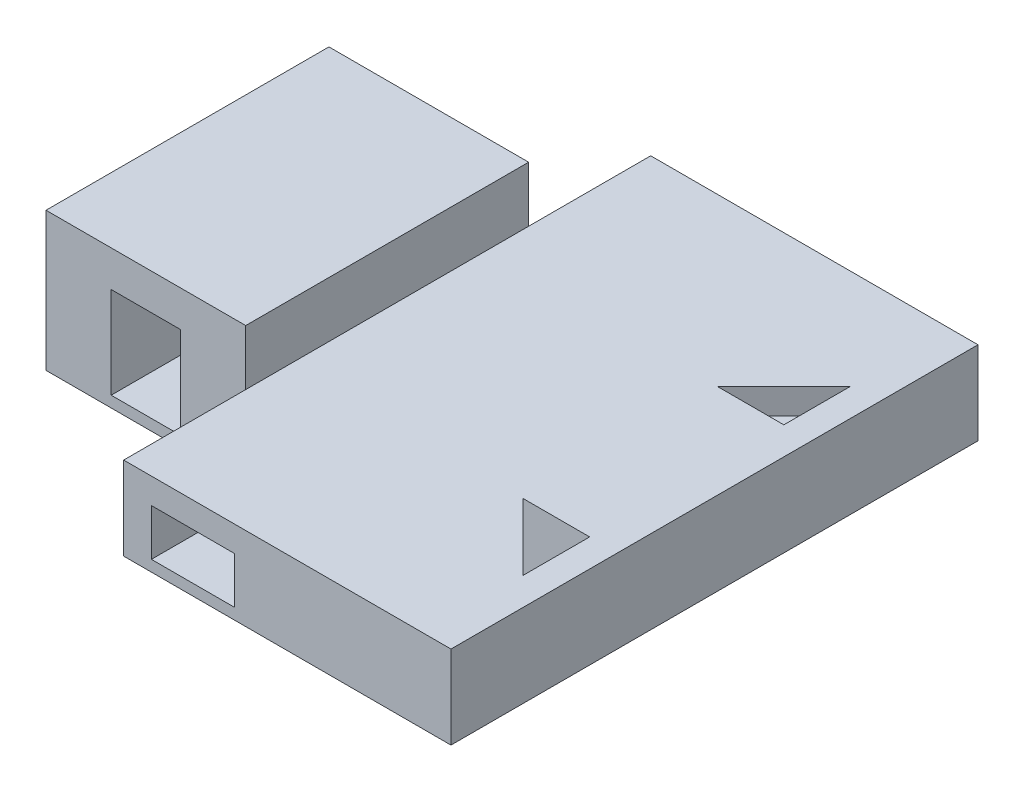
SolidWorks part; units mm, degrees
ref_plane "Front Plane" through (0, 0, 0) normal (0, 0, 1) x (1, 0, 0)
ref_plane "Top Plane" through (0, 0, 0) normal (0, 1, 0) x (1, 0, 0)
ref_plane "Right Plane" through (0, 0, 0) normal (1, 0, 0) x (0, 0, -1)
sketch "Sketch1" plane through (0, 0, 0) normal (0, 1, 0) x (1, 0, 0)
  line L1 (-45, -47.5) -> (45, -47.5)
  line L2 (-45, -47.5) -> (-45, 47.5)
  line L3 (-45, 47.5) -> (45, 47.5)
  line L4 (45, -47.5) -> (45, 47.5)
  line L5 (-45, -47.5) -> (45, 47.5) construction
  line L6 (-45, 47.5) -> (45, -47.5) construction
  point P0 (0, 0)
  dimension "D1" = 95
  dimension "D2" = 90
extrude "Boss-Extrude3" add sketch "Sketch1" along normal blind 15
sketch "Sketch5" plane through (45, 0, 0) normal (1, 0, 0) x (0, 0, -1)
  line L0 (-47.5, 0) -> (47.5, 0) construction
  line L1 (-6.6, 2) -> (8.4, 2)
  line L2 (-6.6, 2) -> (-6.6, 10.4)
  line L3 (-6.6, 10.4) -> (8.4, 10.4)
  line L4 (8.4, 2) -> (8.4, 10.4)
  dimension "D1" = 15
  dimension "D2" = 8.4
  dimension "D3" = 2
extrude "Cut-Extrude3" cut sketch "Sketch5" against normal blind 40
sketch "Sketch7" plane through (45, 0, 0) normal (1, 0, 0) x (0, 0, -1)
  line L1 (-47.5, 0) -> (47.5, 0)
  line L2 (-47.5, 0) -> (-47.5, 15)
  line L3 (-47.5, 15) -> (47.5, 15)
  line L4 (47.5, 0) -> (47.5, 15)
extrude "Boss-Extrude4" add sketch "Sketch7" along normal blind 5
sketch "Sketch10" plane through (0, 15, 0) normal (0, 1, 0) x (1, 0, 0)
  line L0 (50, 47.5) -> (50, -47.5) construction
  line L3 (33, -17.5) -> (45, -17.5)
  line L4 (45, -29.5) -> (45, -17.5)
  line L6 (45, -29.5) -> (33, -17.5)
  dimension "D3" = 5
extrude "Cut-Extrude7" cut sketch "Sketch10" against normal blind 13
sketch "Sketch12" plane through (7.75, 0, -7.75) normal (0.7071, 0, -0.7071) x (-0.7071, 0, -0.7071)
  line L0 (-35.7089, 2) -> (-35.7089, 15) construction
  line L1 (-36.7089, 10.4) -> (-51.7089, 10.4)
  line L2 (-36.7089, 10.4) -> (-36.7089, 2)
  line L3 (-36.7089, 2) -> (-51.7089, 2)
  line L4 (-51.7089, 10.4) -> (-51.7089, 2)
  line L5 (-35.7089, 2) -> (-52.6795, 2) construction
  dimension "D1" = 15
  dimension "D2" = 8.4
  dimension "D3" = 1
  dimension "D4" = 0
extrude "Cut-Extrude8" cut sketch "Sketch12" against normal blind 20
sketch "Sketch13" plane through (0, 15, 0) normal (0, 1, 0) x (1, 0, 0)
  line L0 (50, 47.5) -> (50, -47.5) construction
  line L1 (33, 17.5) -> (45, 17.5)
  line L4 (45, 17.5) -> (45, 29.5)
  line L5 (50, 47.5) -> (-45, 47.5) construction
  line L6 (33, 17.5) -> (45, 29.5)
  dimension "D3" = 5
  dimension "D4" = 18
extrude "Cut-Extrude9" cut sketch "Sketch13" against normal blind 13
sketch "Sketch14" plane through (7.75, 0, 7.75) normal (0.7071, 0, 0.7071) x (0.7071, 0, -0.7071)
  line L0 (35.7089, 2) -> (35.7089, 15) construction
  line L1 (36.7089, 2) -> (51.7089, 2)
  line L2 (36.7089, 2) -> (36.7089, 10.4)
  line L3 (36.7089, 10.4) -> (51.7089, 10.4)
  line L4 (51.7089, 2) -> (51.7089, 10.4)
  line L5 (52.6795, 2) -> (35.7089, 2) construction
  dimension "D1" = 8.4
  dimension "D2" = 15
  dimension "D3" = 1
  dimension "D4" = 0
extrude "Cut-Extrude11" cut sketch "Sketch14" against normal blind 20
sketch "Sketch15" plane through (0, 0, 47.5) normal (0, 0, 1) x (1, 0, 0)
  line L0 (-45, 15) -> (50, 15) construction
  line L1 (-45, 0) -> (-9, 0)
  line L2 (-45, 0) -> (-45, 15)
  line L3 (-45, 15) -> (-9, 15)
  line L4 (-9, 0) -> (-9, 15)
  dimension "D1" = 36
extrude "Cut-Extrude12" cut sketch "Sketch15" against normal blind 22
sketch "Sketch16" plane through (0, 0, -47.5) normal (0, 0, -1) x (-1, 0, 0)
  line L0 (-50, 0) -> (45, 0) construction
  line L1 (45, 15) -> (9, 15)
  line L2 (45, 15) -> (45, 0)
  line L3 (45, 0) -> (9, 0)
  line L4 (9, 15) -> (9, 0)
  dimension "D1" = 36
extrude "Cut-Extrude13" cut sketch "Sketch16" against normal blind 22
sketch "Sketch17" plane through (0, 15, 0) normal (0, 1, 0) x (1, 0, 0)
  line L1 (-45, -25.5) -> (-9, -25.5)
  line L2 (-45, -25.5) -> (-45, 25.5)
  line L3 (-45, 25.5) -> (-9, 25.5)
  line L4 (-9, -25.5) -> (-9, 25.5)
extrude "Boss-Extrude5" add sketch "Sketch17" along normal blind 10
sketch "Sketch18" plane through (0, 0, -25.5) normal (0, 0, -1) x (-1, 0, 0)
  line L0 (9, 0) -> (45, 0) construction
  line L1 (20.75, 2) -> (33.25, 2)
  line L2 (20.75, 2) -> (20.75, 18.5)
  line L3 (20.75, 18.5) -> (33.25, 18.5)
  line L4 (33.25, 2) -> (33.25, 18.5)
  line L5 (45, 0) -> (45, 25) construction
  dimension "D1" = 12.5
  dimension "D2" = 16.5
  dimension "D3" = 2
  dimension "D4" = 11.75
extrude "Cut-Extrude14" cut sketch "Sketch18" against normal blind 100
sketch "Sketch19" plane through (0, 0, -47.5) normal (0, 0, -1) x (-1, 0, 0)
  line L0 (-50, 0) -> (9, 0) construction
  line L1 (-11, 2) -> (4, 2)
  line L2 (-11, 2) -> (-11, 10.4)
  line L3 (-11, 10.4) -> (4, 10.4)
  line L4 (4, 2) -> (4, 10.4)
  line L5 (9, 15) -> (9, 0) construction
  dimension "D1" = 15
  dimension "D2" = 8.4
  dimension "D3" = 2
  dimension "D4" = 5
extrude "Cut-Extrude15" cut sketch "Sketch19" against normal blind 100
sketch "Sketch20" plane through (0, 0, 25.5) normal (0, 0, 1) x (1, 0, 0)
  line L0 (-45, 25) -> (-9, 25) construction
  line L1 (-9, 15) -> (-16.7203, 15)
  line L2 (-9, 15) -> (-9, 25)
  line L3 (-9, 25) -> (-16.7203, 25)
  line L4 (-16.7203, 15) -> (-16.7203, 25)
  dimension "D1" = 4.0297
